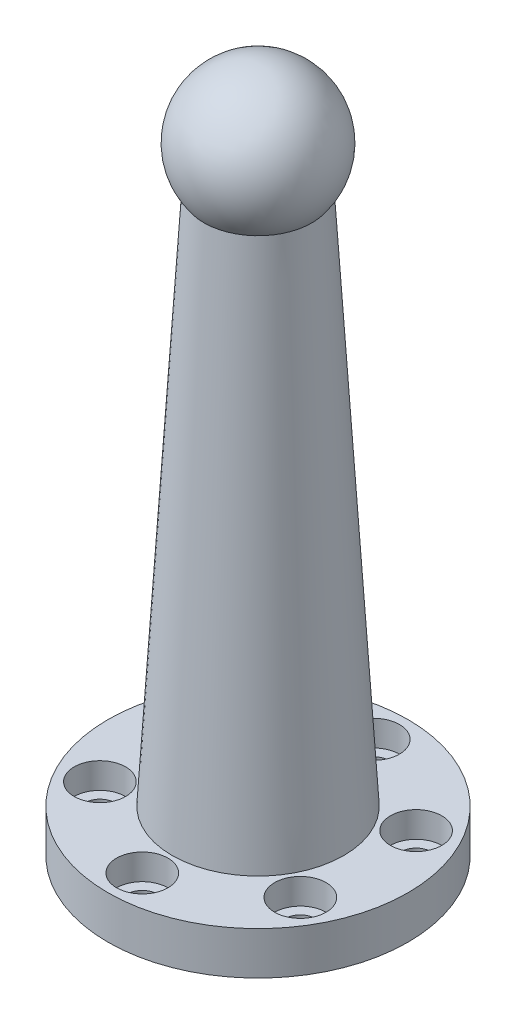
SolidWorks part; units mm, degrees
ref_plane "前视基准面" through (0, 0, 0) normal (0, 0, 1) x (1, 0, 0)
ref_plane "上视基准面" through (0, 0, 0) normal (0, 1, 0) x (1, 0, 0)
ref_plane "右视基准面" through (0, 0, 0) normal (1, 0, 0) x (0, 0, -1)
sketch "草图1" plane through (0, 0, 0) normal (0, 1, 0) x (1, 0, 0)
  circle A0 centre (0, 0) radius 17.5
  circle A1 centre (0, 0) radius 13.5 construction
  circle A2 centre (0, 13.5) radius 1.75
  circle A3 centre (11.6913, 6.75) radius 1.75
  circle A4 centre (11.6913, -6.75) radius 1.75
  circle A5 centre (0, -13.5) radius 1.75
  circle A6 centre (-11.6913, -6.75) radius 1.75
  circle A7 centre (-11.6913, 6.75) radius 1.75
  point P19 (0, 0)
  dimension "D1" = 35
  dimension "D2" = 27
  dimension "D3" = 3.5
  dimension "D4" = 6
extrude "凸台-拉伸1" add sketch "草图1" along normal blind 5
sketch "草图2" plane through (0, 5, 0) normal (0, 1, 0) x (1, 0, 0)
  circle A0 centre (0, 0) radius 13.5 construction
  circle A1 centre (0, 13.5) radius 3
  circle A2 centre (11.6913, 6.75) radius 3
  circle A3 centre (11.6913, -6.75) radius 3
  circle A4 centre (0, -13.5) radius 3
  circle A5 centre (-11.6913, -6.75) radius 3
  circle A6 centre (-11.6913, 6.75) radius 3
  point P19 (0, 0)
  dimension "D1" = 6
  dimension "D2" = 6
extrude "切除-拉伸1" cut sketch "草图2" against normal blind 3
sketch "草图3" plane through (0, 5, 0) normal (0, 1, 0) x (1, 0, 0)
  circle A0 centre (0, 0) radius 10
  dimension "D1" = 20
ref_plane "基准面4" through (0, 72, 0) normal (0, 1, 0) x (1, 0, 0)
sketch "草图6" plane through (0, 72, 0) normal (0, 1, 0) x (1, 0, 0)
  circle A0 centre (0, 0) radius 6
  dimension "D1" = 12
loft "放样1" add profiles "草图3", "草图6"
sketch "草图7" plane through (0, 72, 0) normal (0, 1, 0) x (1, 0, 0)
  line L0 (-8, 0) -> (8, 0) construction
  line L1 (-8, 0) -> (8, 0)
  arc A0 (8, 0) -> (-8, 0) centre (0, 0) ccw
  dimension "D1" = 8
revolve "旋转7" add sketch "草图7" angle 360 about L0
